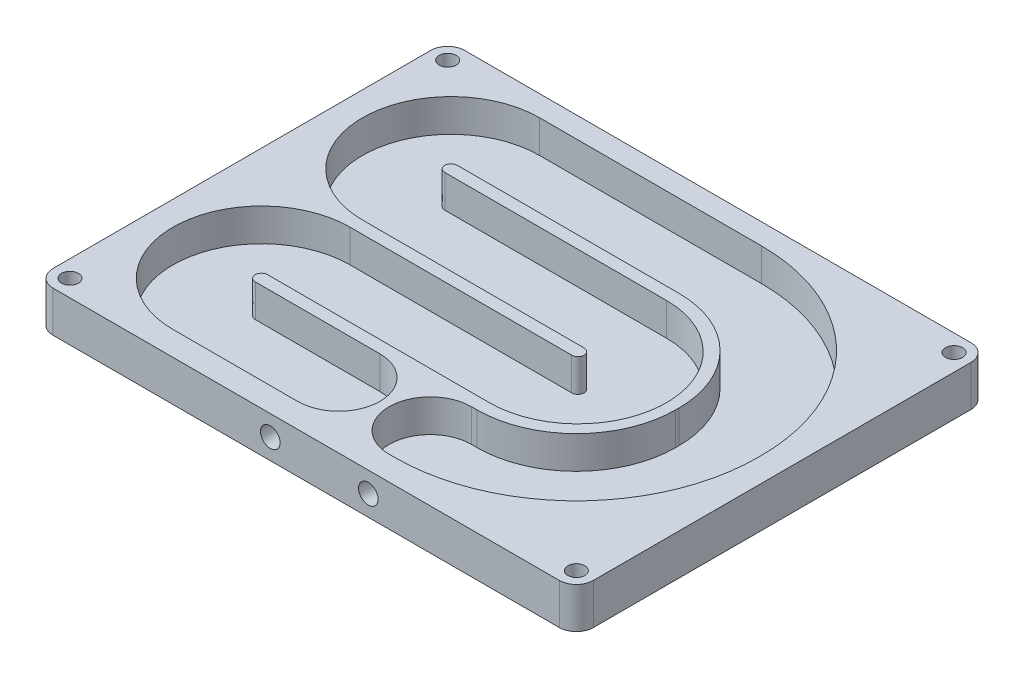
SolidWorks part; units mm, degrees
ref_plane "Front Plane" through (0, 0, 0) normal (0, 0, 1) x (1, 0, 0)
ref_plane "Top Plane" through (0, 0, 0) normal (0, 1, 0) x (1, 0, 0)
ref_plane "Right Plane" through (0, 0, 0) normal (1, 0, 0) x (0, 0, -1)
sketch "Sketch1" plane through (0, 0, 0) normal (0, 1, 0) x (1, 0, 0)
  line L0 (-98.396, 0) -> (98.396, 0)
  line L1 (-105, 6.604) -> (-105, 153.396)
  line L2 (-98.396, 160) -> (98.396, 160)
  line L3 (105, 6.604) -> (105, 153.396)
  arc A0 (-98.396, 0) -> (-105, 6.604) centre (-98.396, 6.604) cw
  arc A1 (98.396, 0) -> (105, 6.604) centre (98.396, 6.604) ccw
  arc A2 (98.396, 160) -> (105, 153.396) centre (98.396, 153.396) cw
  arc A3 (-105, 153.396) -> (-98.396, 160) centre (-98.396, 153.396) cw
  circle A4 centre (-98.396, 6.604) radius 3.302
  circle A5 centre (98.396, 6.604) radius 3.302
  circle A6 centre (98.396, 153.396) radius 3.302
  circle A7 centre (-98.396, 153.396) radius 3.302
  dimension "D1" = 6.604
  dimension "D2" = 6.604
  dimension "D4" = 6.604
  dimension "D8" = 6.604
  dimension "D12" = 6.604
  dimension "D3" = 6.604
  dimension "D5" = 6.604
  dimension "D6" = 6.604
  dimension "D7" = 6.604
  dimension "D9" = 6.604
  dimension "D10" = 6.604
  dimension "D11" = 6.604
  dimension "D13" = 6.604
  dimension "D26" = 210
  dimension "D27" = 160
extrude "Boss-Extrude1" add sketch "Sketch1" along normal blind 15.875
sketch "Sketch2" plane through (0, 15.875, 0) normal (0, 1, 0) x (1, 0, 0)
  line L0 (-79.6, 160) -> (-79.6, 0) construction
  line L1 (0, 160) -> (0, 0) construction
  line L2 (98.396, 160) -> (-98.396, 160) construction
  line L3 (-98.396, 0) -> (98.396, 0) construction
  line L4 (-105, 153.396) -> (-105, 6.604) construction
  line L5 (79.6, 160) -> (79.6, 0) construction
  line L6 (105, 6.604) -> (105, 153.396) construction
  line L7 (79.6, 81.28) -> (79.6, 80.01)
  line L8 (-61.185, 25.4) -> (-12.729, 25.4)
  line L9 (24.99, 135.89) -> (-61.185, 135.89)
  line L10 (-61.185, 99.06) -> (24.99, 99.06)
  line L11 (-61.185, 62.23) -> (24.99, 62.23)
  line L12 (22.831, 160) -> (22.831, 0) construction
  line L15 (22.831, 25.4) -> (24.99, 25.4)
  arc A0 (-61.185, 62.23) -> (-61.185, 25.4) centre (-61.185, 43.815) ccw
  arc A1 (-61.185, 99.06) -> (-61.185, 135.89) centre (-61.185, 117.475) cw
  arc A2 (24.99, 135.89) -> (79.6, 81.28) centre (24.99, 81.28) cw
  arc A3 (24.99, 25.4) -> (79.6, 80.01) centre (24.99, 80.01) ccw
  arc A4 (24.99, 62.23) -> (24.99, 99.06) centre (24.99, 80.645) ccw
  dimension "D7" = 54.61
  dimension "D8" = 54.61
  dimension "D9" = 82.169
  dimension "D1" = 25.4
  dimension "D2" = 25.4
  dimension "D3" = 25.4
  dimension "D4" = 36.83
  dimension "D5" = 36.83
  dimension "D6" = 36.83
  dimension "D10" = 35.56
  dimension "D11" = 80.01
sketch "Sketch3" plane through (0, 15.875, 0) normal (0, 1, 0) x (1, 0, 0)
  line L16 (63.598, 80.01) -> (63.598, 81.28)
  line L17 (63.598, 80.01) -> (63.598, 81.28)
  line L18 (24.99, 119.888) -> (-61.185, 119.888)
  line L19 (24.99, 119.888) -> (-61.185, 119.888)
  line L20 (-61.185, 115.062) -> (24.99, 115.062)
  line L21 (-61.185, 115.062) -> (24.99, 115.062)
  line L68 (22.831, 9.398) -> (24.99, 9.398)
  line L69 (95.602, 80.01) -> (95.602, 81.28)
  line L70 (24.99, 151.892) -> (-61.185, 151.892)
  line L71 (-61.185, 83.058) -> (24.99, 83.058)
  line L72 (24.99, 78.232) -> (-61.185, 78.232)
  line L73 (-61.185, 9.398) -> (-12.729, 9.398)
  line L74 (22.831, 9.398) -> (24.99, 9.398)
  line L75 (95.602, 80.01) -> (95.602, 81.28)
  line L76 (24.99, 151.892) -> (-61.185, 151.892)
  line L77 (-61.185, 83.058) -> (24.99, 83.058)
  line L78 (24.99, 78.232) -> (-61.185, 78.232)
  line L79 (-61.185, 9.398) -> (-12.729, 9.398)
  line L80 (22.831, 41.402) -> (24.99, 41.402)
  line L84 (24.99, 46.228) -> (-61.185, 46.228)
  line L85 (-61.185, 41.402) -> (-12.729, 41.402)
  line L86 (22.831, 41.402) -> (24.99, 41.402)
  line L90 (24.99, 46.228) -> (-61.185, 46.228)
  line L91 (-61.185, 41.402) -> (-12.729, 41.402)
  arc A15 (63.598, 81.28) -> (24.99, 119.888) centre (24.99, 81.28) ccw
  arc A16 (63.598, 81.28) -> (24.99, 119.888) centre (24.99, 81.28) ccw
  arc A17 (-61.185, 119.888) -> (-61.185, 115.062) centre (-61.185, 117.475) ccw
  arc A18 (-61.185, 119.888) -> (-61.185, 115.062) centre (-61.185, 117.475) ccw
  arc A57 (-12.729, 41.402) -> (-12.729, 9.398) centre (-12.729, 25.4) cw
  arc A58 (22.831, 41.402) -> (22.831, 9.398) centre (22.831, 25.4) ccw
  arc A62 (24.99, 9.398) -> (95.602, 80.01) centre (24.99, 80.01) ccw
  arc A63 (95.602, 81.28) -> (24.99, 151.892) centre (24.99, 81.28) ccw
  arc A64 (-61.185, 151.892) -> (-61.185, 83.058) centre (-61.185, 117.475) ccw
  arc A65 (24.99, 78.232) -> (24.99, 83.058) centre (24.99, 80.645) ccw
  arc A66 (-61.185, 78.232) -> (-61.185, 9.398) centre (-61.185, 43.815) ccw
  arc A67 (24.99, 9.398) -> (95.602, 80.01) centre (24.99, 80.01) ccw
  arc A68 (95.602, 81.28) -> (24.99, 151.892) centre (24.99, 81.28) ccw
  arc A69 (-61.185, 151.892) -> (-61.185, 83.058) centre (-61.185, 117.475) ccw
  arc A70 (24.99, 78.232) -> (24.99, 83.058) centre (24.99, 80.645) ccw
  arc A71 (-61.185, 78.232) -> (-61.185, 9.398) centre (-61.185, 43.815) ccw
  arc A72 (24.99, 41.402) -> (63.598, 80.01) centre (24.99, 80.01) ccw
  arc A75 (24.99, 46.228) -> (24.99, 115.062) centre (24.99, 80.645) ccw
  arc A76 (-61.185, 46.228) -> (-61.185, 41.402) centre (-61.185, 43.815) ccw
  arc A77 (24.99, 41.402) -> (63.598, 80.01) centre (24.99, 80.01) ccw
  arc A80 (24.99, 46.228) -> (24.99, 115.062) centre (24.99, 80.645) ccw
  arc A81 (-61.185, 46.228) -> (-61.185, 41.402) centre (-61.185, 43.815) ccw
  dimension "D1" = 16.002
  dimension "D2" = 16.002
extrude "Cut-Extrude1" cut sketch "Sketch3" against normal blind 12.7
sketch "Sketch4" plane through (0, 0, 0) normal (0, 0, 1) x (1, 0, 0)
  line L0 (-105, 7.9375) -> (105, 7.9375) construction
  line L1 (-105, 15.875) -> (-105, 0) construction
  line L2 (105, 15.875) -> (105, 0) construction
  line L3 (5.109, 15.875) -> (5.109, 3.175) construction
  line L4 (-98.396, 15.875) -> (98.396, 15.875) construction
  line L5 (-61.185, 3.175) -> (24.99, 3.175) construction
  circle A0 centre (-13.941, 7.9375) radius 3.81
  circle A1 centre (24.159, 7.9375) radius 3.81
  dimension "D4" = 7.62
  dimension "D5" = 7.62
  dimension "D1" = 19.05
  dimension "D2" = 19.05
  dimension "D7" = 110.109
extrude "Cut-Extrude2" cut sketch "Sketch4" against normal blind 13.97
